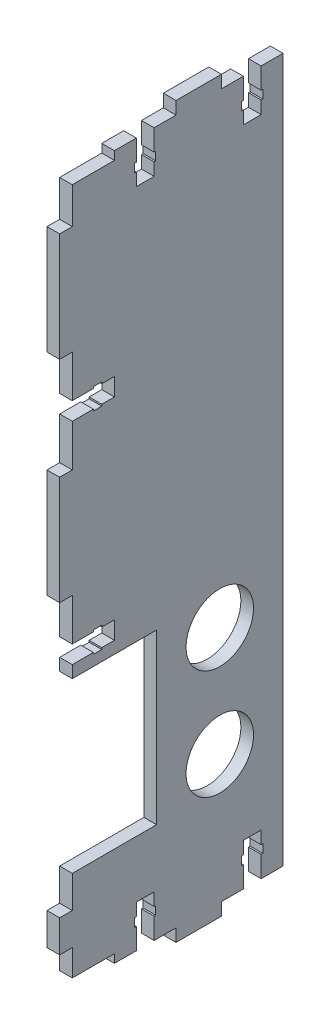
SolidWorks part; units mm, degrees
ref_plane "Front Plane" through (0, 0, 0) normal (0, 0, 1) x (1, 0, 0)
ref_plane "Top Plane" through (0, 0, 0) normal (0, 1, 0) x (1, 0, 0)
ref_plane "Right Plane" through (0, 0, 0) normal (1, 0, 0) x (0, 0, -1)
sketch "Sketch1" plane through (0, 0, 0) normal (1, 0, 0) x (0, 0, -1)
  line L0 (-3, 80.61) -> (-3, 106.39)
  line L1 (0, 0) -> (15.195, 0)
  line L2 (0, 0) -> (0, 8.24)
  line L3 (0, 167) -> (15.195, 167)
  line L4 (50, 0) -> (50, 167)
  line L5 (-3, 106.39) -> (0, 106.39)
  line L6 (0, 23.5) -> (20, 23.5)
  line L7 (20, 23.5) -> (20, 63.5)
  line L8 (20, 63.5) -> (0, 63.5)
  line L9 (0, 80.61) -> (-3, 80.61)
  line L10 (5, 66.39) -> (5, 66)
  line L11 (0, 66.39) -> (5, 66.39)
  line L15 (5, 66) -> (7, 66)
  line L16 (7, 66) -> (7, 66.39)
  line L17 (7, 66.39) -> (10, 66.39)
  line L18 (10, 66.39) -> (10, 70.61)
  line L19 (10, 70.61) -> (7, 70.61)
  line L20 (7, 70.61) -> (7, 71)
  line L21 (7, 71) -> (5, 71)
  line L22 (5, 71) -> (5, 70.61)
  line L23 (5, 70.61) -> (0, 70.61)
  line L24 (5, 159.89) -> (0, 159.89)
  line L25 (0, 8.24) -> (-3, 8.24)
  line L26 (5, 159.5) -> (5, 159.89)
  line L27 (7, 159.5) -> (5, 159.5)
  line L28 (7, 159.89) -> (7, 159.5)
  line L29 (10, 159.89) -> (7, 159.89)
  line L30 (10, 164.11) -> (10, 159.89)
  line L31 (7, 164.11) -> (10, 164.11)
  line L32 (7, 164.5) -> (7, 164.11)
  line L33 (5, 164.5) -> (7, 164.5)
  line L34 (0, 164.11) -> (5, 164.11)
  line L35 (5, 164.11) -> (5, 164.5)
  line L38 (-3, 8.24) -> (-3, 15.87)
  line L48 (-3, 15.87) -> (0, 15.87)
  line L49 (0, 15.87) -> (0, 23.5)
  line L50 (0, 63.5) -> (0, 66.39)
  line L51 (0, 106.39) -> (0, 113.14)
  line L52 (0, 156.39) -> (0, 159.89)
  line L53 (0, 164.11) -> (0, 167)
  line L54 (0, 120.61) -> (0, 124.11)
  line L55 (0, 70.61) -> (0, 80.61)
  line L56 (15.195, 5) -> (14.805, 5)
  line L57 (15.195, 0) -> (15.195, 5)
  line L58 (14.805, 5) -> (14.805, 7)
  line L59 (14.805, 7) -> (15.195, 7)
  line L60 (15.195, 7) -> (15.195, 10)
  line L61 (15.195, 10) -> (19.415, 10)
  line L62 (19.415, 10) -> (19.415, 7)
  line L63 (19.415, 7) -> (19.805, 7)
  line L64 (19.805, 7) -> (19.805, 5)
  line L65 (19.805, 5) -> (19.415, 5)
  line L66 (19.415, 5) -> (19.415, 0)
  line L67 (24.61, -3) -> (35.39, -3)
  line L68 (35.39, -3) -> (35.39, 0)
  line L69 (24.61, 0) -> (24.61, -3)
  line L70 (44.805, 0) -> (50, 0)
  line L71 (40.585, 5) -> (40.585, 0)
  line L72 (40.195, 5) -> (40.585, 5)
  line L73 (40.195, 7) -> (40.195, 5)
  line L74 (40.585, 7) -> (40.195, 7)
  line L75 (40.585, 10) -> (40.585, 7)
  line L76 (44.805, 10) -> (40.585, 10)
  line L77 (44.805, 7) -> (44.805, 10)
  line L78 (45.195, 7) -> (44.805, 7)
  line L79 (45.195, 5) -> (45.195, 7)
  line L80 (44.805, 0) -> (44.805, 5)
  line L81 (44.805, 5) -> (45.195, 5)
  line L82 (44.805, 162) -> (45.195, 162)
  line L83 (44.805, 167) -> (44.805, 162)
  line L84 (45.195, 162) -> (45.195, 160)
  line L85 (45.195, 160) -> (44.805, 160)
  line L86 (44.805, 160) -> (44.805, 157)
  line L87 (44.805, 157) -> (40.585, 157)
  line L88 (40.585, 157) -> (40.585, 160)
  line L89 (40.585, 160) -> (40.195, 160)
  line L90 (40.195, 160) -> (40.195, 162)
  line L91 (40.195, 162) -> (40.585, 162)
  line L92 (40.585, 162) -> (40.585, 167)
  line L93 (24.61, 167) -> (24.61, 170)
  line L94 (35.39, 170) -> (35.39, 167)
  line L95 (24.61, 170) -> (35.39, 170)
  line L96 (19.415, 162) -> (19.415, 167)
  line L97 (19.805, 162) -> (19.415, 162)
  line L98 (19.805, 160) -> (19.805, 162)
  line L99 (19.415, 160) -> (19.805, 160)
  line L100 (19.415, 157) -> (19.415, 160)
  line L101 (15.195, 157) -> (19.415, 157)
  line L102 (15.195, 160) -> (15.195, 157)
  line L103 (14.805, 160) -> (15.195, 160)
  line L104 (14.805, 162) -> (14.805, 160)
  line L105 (15.195, 167) -> (15.195, 162)
  line L106 (15.195, 162) -> (14.805, 162)
  line L107 (35.39, 0) -> (40.585, 0)
  line L108 (19.415, 0) -> (24.61, 0)
  line L109 (44.805, 167) -> (50, 167)
  line L110 (35.39, 167) -> (40.585, 167)
  line L111 (19.415, 167) -> (24.61, 167)
  line L113 (0, 124.11) -> (0, 130.61)
  line L114 (-3, 130.61) -> (0, 130.61)
  line L115 (-3, 130.61) -> (-3, 156.39)
  line L116 (-3, 156.39) -> (0, 156.39)
  line L117 (0, 116.39) -> (0, 113.14)
  line L121 (5, 116.39) -> (0, 116.39)
  line L122 (5, 116) -> (5, 116.39)
  line L123 (7, 116) -> (5, 116)
  line L124 (7, 116.39) -> (7, 116)
  line L125 (10, 116.39) -> (7, 116.39)
  line L126 (10, 120.61) -> (10, 116.39)
  line L127 (7, 120.61) -> (10, 120.61)
  line L128 (7, 121) -> (7, 120.61)
  line L129 (5, 121) -> (7, 121)
  line L130 (0, 120.61) -> (5, 120.61)
  line L131 (5, 120.61) -> (5, 121)
extrude "Boss-Extrude1" add sketch "Sketch1" along normal blind 3
sketch "Sketch2" plane through (3, 0, 0) normal (1, 0, 0) x (0, 0, -1)
  line L0 (0, 2) -> (10, 2)
  line L1 (0, 8.24) -> (0, 0) construction
  line L2 (10, 2) -> (10, 0)
  line L3 (0, 0) -> (15.195, 0) construction
  line L6 (0, 2) -> (0, 0)
  line L7 (0, 0) -> (10, 0)
extrude "Cut-Extrude1" cut sketch "Sketch2" against normal blind 3
sketch "Sketch3" plane through (3, 0, 0) normal (1, 0, 0) x (0, 0, -1)
  line L0 (0, 164.11) -> (0, 159.89)
  line L1 (0, 159.89) -> (5, 159.89)
  line L2 (5, 159.89) -> (5, 159.5)
  line L3 (7, 159.5) -> (5, 159.5) construction
  line L4 (5, 159.5) -> (7, 159.5)
  line L5 (7, 159.5) -> (7, 159.89)
  line L6 (7, 159.89) -> (10, 159.89)
  line L7 (10, 159.89) -> (10, 164.11)
  line L8 (10, 164.11) -> (7, 164.11)
  line L9 (7, 164.11) -> (7, 164.5)
  line L10 (7, 164.5) -> (5, 164.5)
  line L11 (5, 164.5) -> (5, 164.11)
  line L12 (5, 164.11) -> (0, 164.11)
extrude "Boss-Extrude3" add sketch "Sketch3" against normal through all
sketch "Sketch4" plane through (3, 0, 0) normal (1, 0, 0) x (0, 0, -1)
  line L1 (0, 167) -> (10, 167)
  line L2 (0, 167) -> (0, 165)
  line L3 (0, 165) -> (10, 165)
  line L4 (10, 167) -> (10, 165)
extrude "Cut-Extrude2" cut sketch "Sketch4" against normal through all
sketch "Sketch5" plane through (3, 0, 0) normal (1, 0, 0) x (0, 0, -1)
  line L3 (25, 21) -> (45, 21)
  line L4 (25, 21) -> (25, 66)
  line L5 (25, 66) -> (45, 66)
  line L6 (45, 21) -> (45, 66)
  circle A0 centre (35, 30.5) radius 8
  circle A1 centre (35, 56.5) radius 8
extrude "Cut-Extrude3" cut sketch "Sketch5" against normal blind 10 contours A0 | A1
